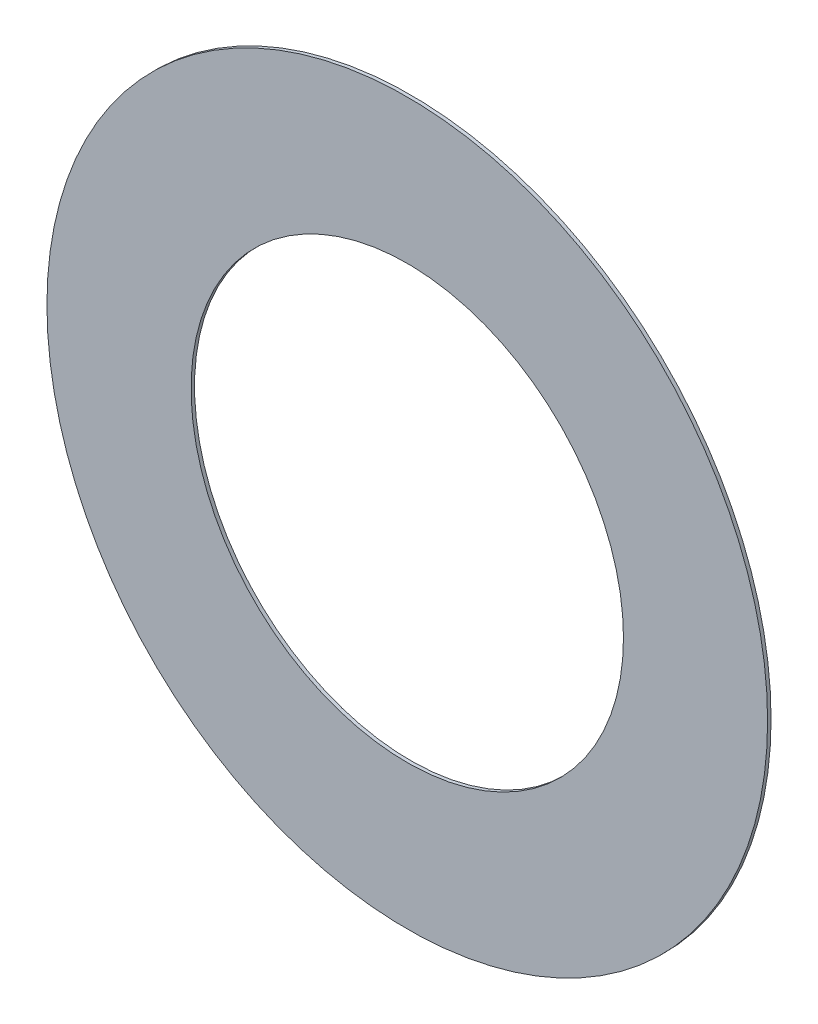
SolidWorks part; units mm, degrees
material "AISI 1020"
ref_plane "Front Plane" through (0, 0, 0) normal (0, 0, 1) x (1, 0, 0)
ref_plane "Top Plane" through (0, 0, 0) normal (0, 1, 0) x (1, 0, 0)
ref_plane "Right Plane" through (0, 0, 0) normal (1, 0, 0) x (0, 0, -1)
sketch "Sketch1" plane through (0, 0, 0) normal (0, 0, 1) x (1, 0, 0)
  circle A0 centre (0, 0) radius 4.7625
  circle A1 centre (0, 0) radius 7.9375
  dimension "D1" = 9.525
  dimension "D2" = 15.875
extrude "Boss-Extrude1" add sketch "Sketch1" along normal blind 0.0762
